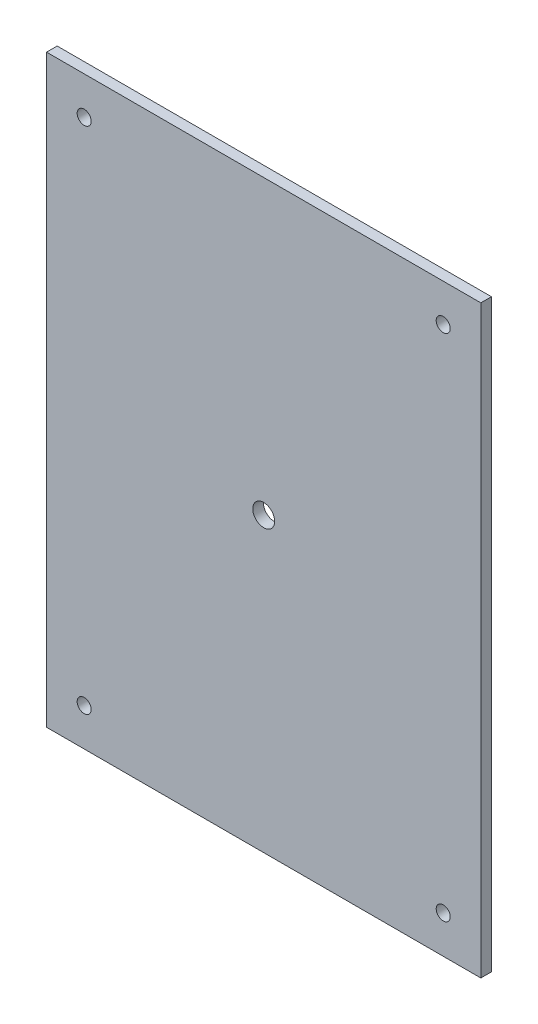
SolidWorks part; units mm, degrees
ref_plane "Front Plane" through (0, 0, 0) normal (0, 0, 1) x (1, 0, 0)
ref_plane "Top Plane" through (0, 0, 0) normal (0, 1, 0) x (1, 0, 0)
ref_plane "Right Plane" through (0, 0, 0) normal (1, 0, 0) x (0, 0, -1)
sketch "Sketch1" plane through (0, 0, 0) normal (0, 0, 1) x (1, 0, 0)
  line L1 (0, 0) -> (-259.8, 0)
  line L6 (-259.8, 0) -> (-259.8, 349.8)
  line L7 (-259.8, 349.8) -> (0, 349.8)
  line L8 (0, 349.8) -> (0, 0)
  line L17 (0, 0) -> (31.9541, 0) construction
  line L18 (31.9541, 0) -> (31.9541, 45) construction
  line L19 (31.9541, 45) -> (31.9541, 304.8) construction
  line L20 (31.9541, 304.8) -> (31.9541, 349.8) construction
  line L21 (31.9541, 349.8) -> (0, 349.8) construction
  line L22 (-259.8, 0) -> (-259.8, -43.8956) construction
  line L23 (45, -43.8956) -> (0, -43.8956) construction
  line L24 (0, -43.8956) -> (-259.8, -43.8956) construction
  line L25 (-259.8, -43.8956) -> (-304.8, -43.8956) construction
  line L26 (0, 0) -> (0, -43.8956) construction
  point P18 (31.9541, 22.5)
  point P23 (31.9541, 327.3)
  point P24 (-282.3, -43.8956)
  point P29 (22.5, -43.8956)
  dimension "D1" = 45
  dimension "D2" = 45
  dimension "D3" = 304.8
  dimension "D4" = 349.8
  dimension "D5" = 45
  dimension "D6" = 45
  dimension "D7" = 304.8
  dimension "D8" = 259.8
extrude "Boss-Extrude1" add sketch "Sketch1" along normal blind 6.35
hole_wizard "1/2 Clearance Hole1" positions "Sketch2" profile "Sketch3" hole size "1/2" standard "ANSI Inch"
sketch "Sketch2" plane through (0, 0, 6.35) normal (0, 0, 1) x (1, 0, 0)
  line L2 (-129.9, 349.8) -> (-129.9, 0) construction
  line L3 (0, 349.8) -> (-259.8, 349.8) construction
  line L4 (-259.8, 0) -> (0, 0) construction
  point P0 (-129.9, 174.9)
  point P14 (-153.0362, 174.9)
  point P15 (-129.9, 349.8)
sketch "Sketch3" plane through (-129.9, 174.9, 6.35) normal (1, 0, 0) x (0, -1, 0)
  line L0 (0, 0) -> (0, 26.2865)
  line L1 (0, 26.2865) -> (6.5481, 22.352)
  line L2 (6.5481, 22.352) -> (6.5481, 0)
  line L5 (6.5481, 0) -> (0, 0)
  line L10 (0, 26.2865) -> (-6.5481, 22.352) construction
  line L11 (0, -6.35) -> (0, 107.95) construction
  dimension "Hole Dia." = 13.0962
  dimension "Hole Depth" = 22.352
  dimension "Drill Angle" = 118
hole_wizard "M8 Clearance Hole1" positions "Sketch4" profile "Sketch5" hole size "M8" standard "ANSI Metric"
sketch "Sketch4" plane through (0, 0, 6.35) normal (0, 0, 1) x (1, 0, 0)
  line L0 (-237.3, 22.5) -> (-237.3, 327.3) construction
  line L1 (-237.3, 327.3) -> (-22.5, 327.3) construction
  line L2 (-22.5, 327.3) -> (-22.5, 22.5) construction
  line L3 (-22.5, 22.5) -> (-237.3, 22.5) construction
  line L6 (0, 349.8) -> (-259.8, 349.8) construction
  line L9 (-129.9, 327.3) -> (-129.9, 349.8) construction
  line L10 (-22.5, 174.9) -> (0, 174.9) construction
  line L11 (0, 0) -> (0, 349.8) construction
  point P0 (-237.3, 327.3)
  point P2 (-22.5, 327.3)
  point P4 (-22.5, 22.5)
  point P6 (-237.3, 22.5)
  dimension "D2" = 22.5
  dimension "D1" = 22.5
sketch "Sketch5" plane through (-237.3, 327.3, 6.35) normal (1, 0, 0) x (0, -1, 0)
  line L0 (0, 0) -> (0, 78.7236)
  line L1 (0, 78.7236) -> (4.2, 76.2)
  line L2 (4.2, 76.2) -> (4.2, 0)
  line L5 (4.2, 0) -> (0, 0)
  line L10 (0, 78.7236) -> (-4.2, 76.2) construction
  line L11 (0, -6.35) -> (0, 107.95) construction
  dimension "Hole Dia." = 8.4
  dimension "Hole Depth" = 76.2
  dimension "Drill Angle" = 118
equation "\"D2@Sketch1\"=\"D1@Sketch1\""
equation "\"D5@Sketch1\"=\"D1@Sketch1\""
equation "\"D6@Sketch1\"=\"D1@Sketch1\""
equation "\"D1@Sketch4\"=\"D2@Sketch4\""
